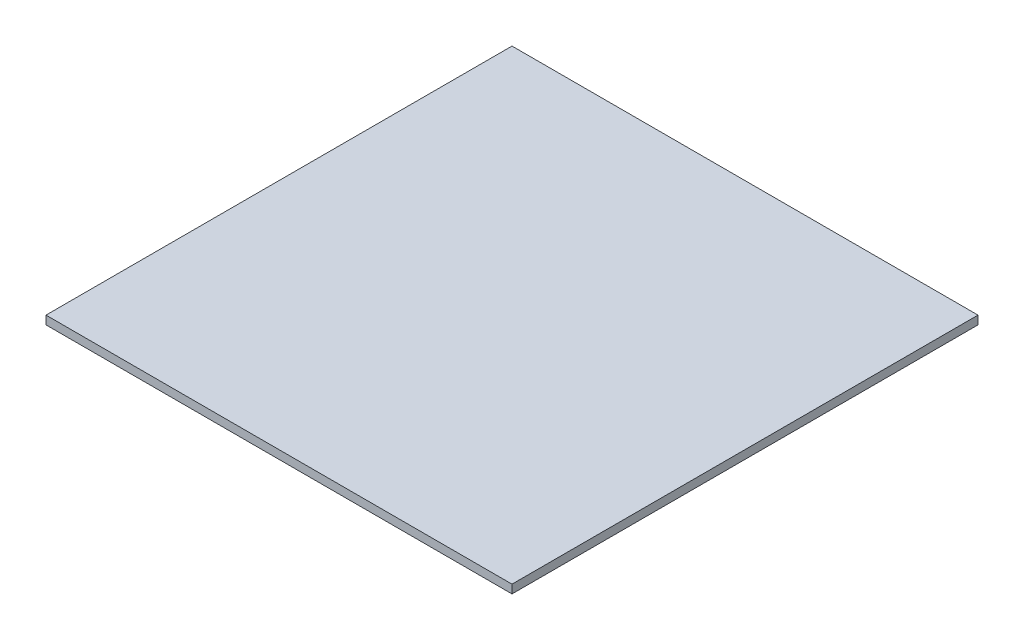
SolidWorks part; units mm, degrees
ref_plane "Front Plane" through (0, 0, 0) normal (0, 0, 1) x (1, 0, 0)
ref_plane "Top Plane" through (0, 0, 0) normal (0, 1, 0) x (1, 0, 0)
ref_plane "Right Plane" through (0, 0, 0) normal (1, 0, 0) x (0, 0, -1)
sketch "Sketch1" plane through (0, 0, 0) normal (0, 1, 0) x (1, 0, 0)
  line L1 (304.8, -304.8) -> (-304.8, -304.8)
  line L2 (304.8, -304.8) -> (304.8, 304.8)
  line L3 (304.8, 304.8) -> (-304.8, 304.8)
  line L4 (-304.8, -304.8) -> (-304.8, 304.8)
  line L5 (304.8, -304.8) -> (-304.8, 304.8) construction
  line L6 (304.8, 304.8) -> (-304.8, -304.8) construction
  point P0 (0, 0)
extrude "Boss-Extrude1" add sketch "Sketch1" along normal blind 11.1125
